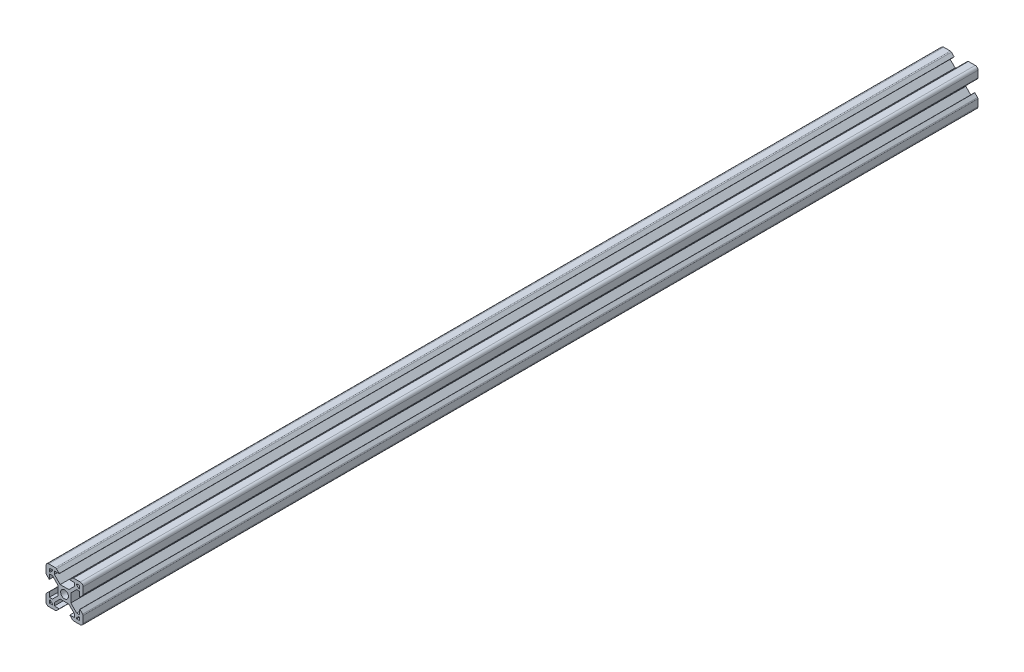
SolidWorks part; units mm, degrees
ref_plane "Front Plane" through (0, 0, 0) normal (0, 0, 1) x (1, 0, 0)
ref_plane "Top Plane" through (0, 0, 0) normal (0, 1, 0) x (1, 0, 0)
ref_plane "Right Plane" through (0, 0, 0) normal (1, 0, 0) x (0, 0, -1)
sketch "Sketch2" plane through (0, 0, 0) normal (0, 0, 1) x (1, 0, 0)
  line L0 (-8.2, 2.89) -> (-8.2, 5.5)
  line L1 (-2.1, 0) -> (-10, 0) construction
  line L2 (0, 2.1) -> (0, 10) construction
  line L3 (-4.9072, 10) -> (-8.5, 10)
  line L4 (-10, 4.9072) -> (-10, 8.5)
  line L5 (-2.1, 0) -> (-3.4, 0) construction
  line L6 (0, 2.1) -> (0, 3.4) construction
  line L7 (0, 3.4) -> (-2.3393, 3.4)
  line L8 (-3.4, 0) -> (-3.4, 2.3393)
  line L9 (-2.89, 8.2) -> (-5.5, 8.2)
  line L10 (-6.57, 8.2) -> (-6.57, 7.66)
  line L11 (-8.2, 6.57) -> (-7.66, 6.57)
  line L12 (-5.5, 8.2) -> (-5.5, 6.5607)
  line L13 (-6.5607, 5.5) -> (-8.2, 5.5)
  line L14 (-8.2, 8.2) -> (-1.4849, 1.4849) construction
  line L15 (-6.5607, 5.5) -> (-3.4, 2.3393)
  line L16 (-5.5, 6.5607) -> (-2.3393, 3.4)
  line L17 (-7.66, 6.57) -> (-6.57, 7.66)
  line L18 (-8.7303, 7.6697) -> (-0.5303, -0.5303) construction
  line L19 (-7.6697, 8.7303) -> (0.5303, 0.5303) construction
  line L20 (-8.2, 8.2) -> (0, 0) construction
  line L21 (-8.2, 6.57) -> (-8.2, 8.2)
  line L22 (-8.2, 0) -> (-8.2, 8.2) construction
  line L23 (-6.57, 8.2) -> (-8.2, 8.2)
  line L24 (0, 8.2) -> (-8.2, 8.2) construction
  line L25 (-10, 0) -> (-10, 10) construction
  line L26 (0, 10) -> (-10, 10) construction
  line L27 (-2.89, 8.31) -> (-2.89, 8.2)
  line L29 (-8.31, 2.89) -> (-8.2, 2.89)
  line L30 (-4.3486, 9.7686) -> (-2.89, 8.31)
  line L31 (-8.31, 2.89) -> (-9.7686, 4.3486)
  arc A0 (0, 2.1) -> (-2.1, 0) centre (0, 0) ccw
  arc A1 (-10, 8.5) -> (-8.5, 10) centre (-8.5, 8.5) cw
  arc A2 (-9.7686, 4.3486) -> (-10, 4.9072) centre (-9.21, 4.9072) cw
  arc A3 (-4.3486, 9.7686) -> (-4.9072, 10) centre (-4.9072, 9.21) ccw
  point P29 (-10, 10)
  point P39 (-10, 4.58)
  point P42 (-4.58, 10)
  dimension "D3" = 2.1
  dimension "D15" = 1.5
  dimension "D22" = 0.79
  dimension "D1" = 10
  dimension "D2" = 10
  dimension "D4" = 1.8
  dimension "D5" = 3.43
  dimension "D6" = 3.43
  dimension "D7" = 0.54
  dimension "D8" = 0.54
  dimension "D9" = 1.07
  dimension "D10" = 1.07
  dimension "D11" = 3.4
  dimension "D12" = 3.4
  dimension "D16" = 7.11
  dimension "D17" = 0.11
  dimension "D18" = 1.69
  dimension "D19" = 0.11
  dimension "D20" = 7.11
  dimension "D21" = 1.69
  dimension "D13" = 0.75
  dimension "D14" = 0.75
sketch "Sketch6" plane through (0, 0, 0) normal (0, 0, 1) x (1, 0, 0)
  line L0 (-3.4, 0) -> (-3.4, 2.3393) construction
  line L1 (-6.5607, 5.5) -> (-3.4, 2.3393) construction
  line L2 (-6.5607, 5.5) -> (-8.2, 5.5) construction
  line L3 (-8.2, 2.89) -> (-8.2, 5.5) construction
  line L4 (-8.31, 2.89) -> (-8.2, 2.89) construction
  line L5 (-7.66, 6.57) -> (-6.57, 7.66)
  line L6 (-6.57, 7.66) -> (-6.57, 8.2)
  line L7 (-6.57, 8.2) -> (-8.2, 8.2)
  line L8 (-8.2, 8.2) -> (-8.2, 6.57)
  line L9 (-8.2, 6.57) -> (-7.66, 6.57)
  line L10 (-7.66, 6.57) -> (-6.57, 7.66)
  line L11 (-6.57, 7.66) -> (-6.57, 8.2)
  line L12 (-6.57, 8.2) -> (-8.2, 8.2)
  line L13 (-8.2, 8.2) -> (-8.2, 6.57)
  line L14 (-8.2, 6.57) -> (-7.66, 6.57)
  line L15 (-8.31, 2.89) -> (-9.7686, 4.3486) construction
  line L16 (-10, 4.9072) -> (-10, 8.5) construction
  line L17 (-4.9072, 10) -> (-8.5, 10) construction
  line L18 (-4.3486, 9.7686) -> (-2.89, 8.31) construction
  line L19 (-2.89, 8.31) -> (-2.89, 8.2) construction
  line L20 (-2.89, 8.2) -> (-5.5, 8.2) construction
  line L21 (-5.5, 8.2) -> (-5.5, 6.5607) construction
  line L22 (-5.5, 6.5607) -> (-2.3393, 3.4) construction
  line L23 (0, 3.4) -> (-2.3393, 3.4) construction
  line L24 (-3.4, -2.3393) -> (-3.4, 2.3393)
  line L25 (-6.5607, 5.5) -> (-3.4, 2.3393)
  line L26 (-6.5607, 5.5) -> (-8.2, 5.5)
  line L27 (-8.2, 2.89) -> (-8.2, 5.5)
  line L28 (-8.31, 2.89) -> (-8.2, 2.89)
  line L29 (-8.31, 2.89) -> (-9.7686, 4.3486)
  line L30 (-10, 4.9072) -> (-10, 8.5)
  line L31 (-4.9072, 10) -> (-8.5, 10)
  line L32 (-4.3486, 9.7686) -> (-2.89, 8.31)
  line L33 (-2.89, 8.31) -> (-2.89, 8.2)
  line L34 (-2.89, 8.2) -> (-5.5, 8.2)
  line L35 (-5.5, 8.2) -> (-5.5, 6.5607)
  line L36 (-5.5, 6.5607) -> (-2.3393, 3.4)
  line L37 (2.3393, 3.4) -> (-2.3393, 3.4)
  line L38 (0, 2.1) -> (0, 10) construction
  line L39 (-2.1, 0) -> (-10, 0) construction
  line L40 (0, 2.1) -> (0, 10) construction
  line L41 (-2.1, 0) -> (-10, 0) construction
  line L42 (2.1, 0) -> (10, 0) construction
  line L43 (5.5, 6.5607) -> (2.3393, 3.4)
  line L44 (5.5, 8.2) -> (5.5, 6.5607)
  line L45 (2.89, 8.2) -> (5.5, 8.2)
  line L46 (2.89, 8.31) -> (2.89, 8.2)
  line L47 (4.3486, 9.7686) -> (2.89, 8.31)
  line L48 (4.9072, 10) -> (8.5, 10)
  line L49 (10, 4.9072) -> (10, 8.5)
  line L50 (8.31, 2.89) -> (9.7686, 4.3486)
  line L51 (8.31, 2.89) -> (8.2, 2.89)
  line L52 (8.2, 2.89) -> (8.2, 5.5)
  line L53 (6.5607, 5.5) -> (8.2, 5.5)
  line L54 (6.5607, 5.5) -> (3.4, 2.3393)
  line L55 (3.4, -2.3393) -> (3.4, 2.3393)
  line L56 (8.2, 6.57) -> (7.66, 6.57)
  line L57 (8.2, 8.2) -> (8.2, 6.57)
  line L58 (6.57, 8.2) -> (8.2, 8.2)
  line L59 (6.57, 7.66) -> (6.57, 8.2)
  line L60 (7.66, 6.57) -> (6.57, 7.66)
  line L61 (0, -2.1) -> (0, -10) construction
  line L62 (7.66, -6.57) -> (6.57, -7.66)
  line L63 (6.57, -7.66) -> (6.57, -8.2)
  line L64 (6.57, -8.2) -> (8.2, -8.2)
  line L65 (8.2, -8.2) -> (8.2, -6.57)
  line L66 (8.2, -6.57) -> (7.66, -6.57)
  line L67 (6.5607, -5.5) -> (3.4, -2.3393)
  line L68 (6.5607, -5.5) -> (8.2, -5.5)
  line L69 (8.2, -2.89) -> (8.2, -5.5)
  line L70 (8.31, -2.89) -> (8.2, -2.89)
  line L71 (8.31, -2.89) -> (9.7686, -4.3486)
  line L72 (10, -4.9072) -> (10, -8.5)
  line L73 (4.9072, -10) -> (8.5, -10)
  line L74 (4.3486, -9.7686) -> (2.89, -8.31)
  line L75 (2.89, -8.31) -> (2.89, -8.2)
  line L76 (2.89, -8.2) -> (5.5, -8.2)
  line L77 (5.5, -8.2) -> (5.5, -6.5607)
  line L78 (5.5, -6.5607) -> (2.3393, -3.4)
  line L79 (2.3393, -3.4) -> (-2.3393, -3.4)
  line L80 (-5.5, -6.5607) -> (-2.3393, -3.4)
  line L81 (-5.5, -8.2) -> (-5.5, -6.5607)
  line L82 (-2.89, -8.2) -> (-5.5, -8.2)
  line L83 (-2.89, -8.31) -> (-2.89, -8.2)
  line L84 (-4.3486, -9.7686) -> (-2.89, -8.31)
  line L85 (-4.9072, -10) -> (-8.5, -10)
  line L86 (-10, -4.9072) -> (-10, -8.5)
  line L87 (-8.31, -2.89) -> (-9.7686, -4.3486)
  line L88 (-8.31, -2.89) -> (-8.2, -2.89)
  line L89 (-8.2, -2.89) -> (-8.2, -5.5)
  line L90 (-6.5607, -5.5) -> (-8.2, -5.5)
  line L91 (-6.5607, -5.5) -> (-3.4, -2.3393)
  line L92 (-8.2, -6.57) -> (-7.66, -6.57)
  line L93 (-8.2, -8.2) -> (-8.2, -6.57)
  line L94 (-6.57, -8.2) -> (-8.2, -8.2)
  line L95 (-6.57, -7.66) -> (-6.57, -8.2)
  line L96 (-7.66, -6.57) -> (-6.57, -7.66)
  arc A0 (0, 2.1) -> (-2.1, 0) centre (0, 0) ccw construction
  arc A1 (-10, 4.9072) -> (-9.7686, 4.3486) centre (-9.21, 4.9072) ccw construction
  arc A2 (-8.5, 10) -> (-10, 8.5) centre (-8.5, 8.5) ccw construction
  arc A3 (-4.3486, 9.7686) -> (-4.9072, 10) centre (-4.9072, 9.21) ccw construction
  circle A4 centre (0, 0) radius 2.1
  arc A5 (-10, 4.9072) -> (-9.7686, 4.3486) centre (-9.21, 4.9072) ccw
  arc A6 (-8.5, 10) -> (-10, 8.5) centre (-8.5, 8.5) ccw
  arc A7 (-4.3486, 9.7686) -> (-4.9072, 10) centre (-4.9072, 9.21) ccw
  arc A8 (4.3486, 9.7686) -> (4.9072, 10) centre (4.9072, 9.21) cw
  arc A9 (8.5, 10) -> (10, 8.5) centre (8.5, 8.5) cw
  arc A10 (10, 4.9072) -> (9.7686, 4.3486) centre (9.21, 4.9072) cw
  arc A11 (10, -4.9072) -> (9.7686, -4.3486) centre (9.21, -4.9072) ccw
  arc A12 (8.5, -10) -> (10, -8.5) centre (8.5, -8.5) ccw
  arc A13 (4.3486, -9.7686) -> (4.9072, -10) centre (4.9072, -9.21) ccw
  arc A14 (-4.3486, -9.7686) -> (-4.9072, -10) centre (-4.9072, -9.21) cw
  arc A15 (-8.5, -10) -> (-10, -8.5) centre (-8.5, -8.5) cw
  arc A16 (-10, -4.9072) -> (-9.7686, -4.3486) centre (-9.21, -4.9072) cw
  point P85 (3.4, 0)
  dimension "D1" = 0
extrude "Boss-Extrude1" add sketch "Sketch6" against normal blind 483
